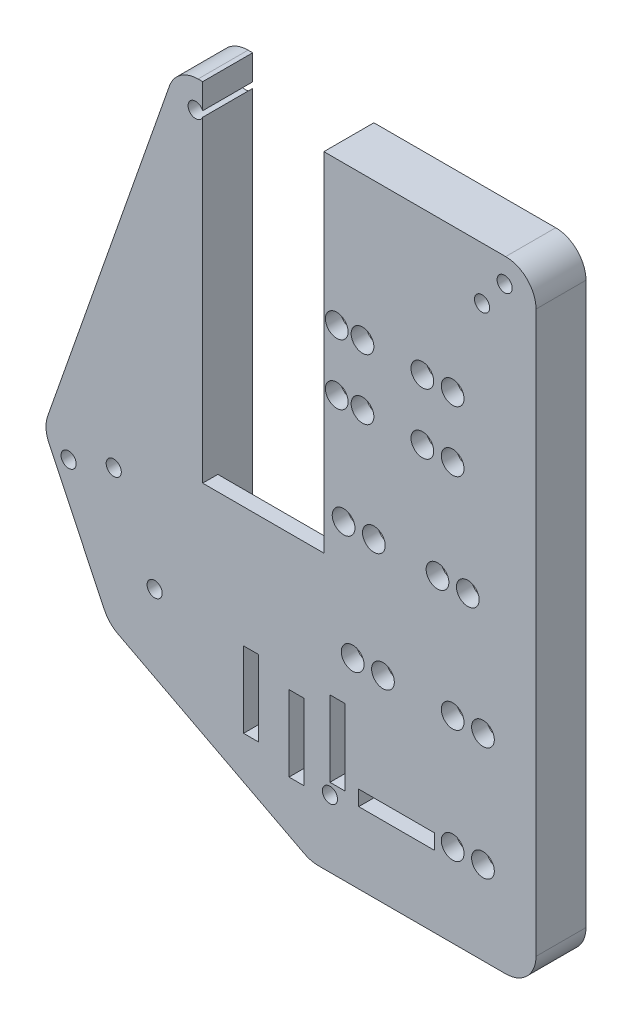
SolidWorks part; units mm, degrees
ref_plane "Front Plane" through (0, 0, 0) normal (0, 0, 1) x (1, 0, 0)
ref_plane "Top Plane" through (0, 0, 0) normal (0, 1, 0) x (1, 0, 0)
ref_plane "Right Plane" through (0, 0, 0) normal (1, 0, 0) x (0, 0, -1)
sketch "Sketch1" plane through (0, 0, 0) normal (0, 0, 1) x (1, 0, 0)
  line L6 (-20.066, -57.15) -> (46.99, -57.15) construction
  line L7 (-12.446, -73.152) -> (46.99, -73.152) construction
  line L8 (-3.3141, 6.35) -> (48.26, 6.35)
  line L9 (53.34, 1.27) -> (53.34, -92.71)
  line L10 (48.26, -97.79) -> (16.847, -97.79)
  line L16 (-8.1072, 2.9529) -> (-28.5162, -55.1739)
  line L18 (-20.066, -57.15) -> (-29.21, -57.15) construction
  line L26 (0, 0) -> (46.99, 0) construction
  line L27 (46.99, 0) -> (46.99, -88.9) construction
  line L28 (46.99, -88.9) -> (17.78, -88.9) construction
  line L29 (17.78, -88.9) -> (-12.446, -73.152) construction
  line L30 (-12.446, -73.152) -> (-20.066, -57.15) construction
  line L31 (-20.066, -57.15) -> (0, 0) construction
  line L32 (46.99, -57.15) -> (46.99, -88.9) construction
  line L33 (17.78, -88.9) -> (15.603, -97.79) construction
  line L34 (-12.446, -73.152) -> (-17.9301, -78.4424) construction
  line L35 (14.4997, -97.2152) -> (-16.7505, -80.9336)
  line L36 (-28.3096, -59.0409) -> (-18.9898, -78.6124)
  arc A0 (53.34, -92.71) -> (48.26, -97.79) centre (48.26, -92.71) cw
  arc A1 (14.4997, -97.2152) -> (16.847, -97.79) centre (16.847, -92.71) ccw
  arc A2 (-16.7505, -80.9336) -> (-18.9898, -78.6124) centre (-14.4033, -76.4284) cw
  arc A3 (-28.5162, -55.1739) -> (-28.3096, -59.0409) centre (-23.723, -56.8568) ccw
  arc A4 (-8.1072, 2.9529) -> (-3.3141, 6.35) centre (-3.3141, 1.27) cw
  arc A5 (48.26, 6.35) -> (53.34, 1.27) centre (48.26, 1.27) cw
  point P13 (53.34, -97.79)
  point P30 (53.34, 6.35)
  dimension "D8" = 5.08
  dimension "D1" = 88.9
  dimension "D2" = 29.21
  dimension "D3" = 59.436
  dimension "D4" = 67.056
  dimension "D5" = 104.14
  dimension "D6" = 82.55
  dimension "D7" = 46.99
  dimension "D13" = 103.76
  dimension "D17" = 108.51
extrude "Boss-Extrude1" add sketch "Sketch1" along normal blind 2.54
sketch "Sketch3" plane through (0, 0, 0) normal (0, 0, 1) x (1, 0, 0)
  line L8 (0, 0) -> (46.99, 0) construction
  line L9 (46.99, 0) -> (46.99, -88.9) construction
  line L10 (46.99, -88.9) -> (17.78, -88.9) construction
  line L11 (17.78, -88.9) -> (-12.446, -73.152) construction
  line L12 (-12.446, -73.152) -> (-20.066, -57.15) construction
  line L13 (-20.066, -57.15) -> (0, 0) construction
sketch "Sketch4" plane through (0, 0, 0) normal (0, 0, -1) x (-1, 0, 0)
  line L0 (-46.99, 0) -> (-46.99, -88.9) construction
  line L1 (0, 0) -> (-46.99, 0) construction
  line L2 (-46.99, -88.9) -> (-17.78, -88.9) construction
  line L8 (-17.78, -1.143) -> (2.54, -1.143)
  line L9 (-17.78, -1.143) -> (-17.78, -51.943)
  line L10 (-17.78, -51.943) -> (2.54, -51.943)
  line L11 (2.54, -1.143) -> (2.54, -51.943)
  circle A0 centre (-39.37, -17.78) radius 1.905
  circle A1 centre (-34.29, -17.78) radius 1.905
  circle A2 centre (-39.37, -27.94) radius 1.905
  circle A3 centre (-34.29, -27.94) radius 1.905
  circle A4 centre (-41.91, -45.72) radius 1.905
  circle A5 centre (-36.83, -45.72) radius 1.905
  circle A6 centre (-44.45, -64.77) radius 1.905
  circle A7 centre (-39.37, -64.77) radius 1.905
  circle A8 centre (-44.45, -83.82) radius 1.905
  circle A9 centre (-39.37, -83.82) radius 1.905
  circle A10 centre (-24.257, -17.78) radius 1.905
  circle A11 centre (-19.939, -17.78) radius 1.905
  circle A12 centre (-24.257, -27.94) radius 1.905
  circle A13 centre (-19.939, -27.94) radius 1.905
  circle A14 centre (-26.162, -45.72) radius 1.905
  circle A15 centre (-21.082, -45.72) radius 1.905
  circle A16 centre (-27.686, -64.77) radius 1.905
  circle A17 centre (-22.606, -64.77) radius 1.905
  point P18 (0, 0)
  dimension "D6" = 3.81
  dimension "D7" = 17.78
  dimension "D11" = 3.81
  dimension "D12" = 3.81
  dimension "D16" = 3.81
  dimension "D17" = 3.81
  dimension "D21" = 3.81
  dimension "D22" = 3.81
  dimension "D30" = 3.81
  dimension "D31" = 3.81
  dimension "D35" = 3.81
  dimension "D36" = 3.81
  dimension "D40" = 3.81
  dimension "D41" = 3.81
  dimension "D45" = 3.81
  dimension "D46" = 3.81
  dimension "D3" = 5.08
  dimension "D5" = 7.62
  dimension "D8" = 5.08
  dimension "D9" = 27.94
  dimension "D10" = 17.78
  dimension "D13" = 5.08
  dimension "D14" = 27.94
  dimension "D15" = 17.78
  dimension "D18" = 5.08
  dimension "D19" = 22.733
  dimension "D20" = 17.78
  dimension "D23" = 5.08
  dimension "D24" = 27.94
  dimension "D25" = 27.051
  dimension "D26" = 50.8
  dimension "D27" = 20.32
  dimension "D28" = 27.94
  dimension "D29" = 45.72
  dimension "D32" = 4.318
  dimension "D33" = 10.16
  dimension "D34" = 5.08
  dimension "D37" = 4.318
  dimension "D38" = 45.72
  dimension "D39" = 45.72
  dimension "D42" = 5.08
  dimension "D43" = 20.828
  dimension "D44" = 2.54
  dimension "D47" = 5.08
  dimension "D48" = 24.13
  dimension "D49" = 2.54
  dimension "D50" = 5.08
  dimension "D51" = 5.08
  dimension "D52" = 24.13
  dimension "D53" = 24.13
  dimension "D54" = 19.304
  dimension "D55" = 24.13
  dimension "D57" = 1.143
  dimension "D58" = 29.21
extrude "Cut-Extrude2" cut sketch "Sketch4" against normal blind 25.4
sketch "Sketch5" plane through (0, 0, 2.54) normal (0, 0, 1) x (1, 0, 0)
  line L0 (-2.54, -1.143) -> (-2.54, 6.35)
  line L1 (48.26, 6.35) -> (-3.3141, 6.35) construction
  line L2 (17.78, -1.143) -> (17.78, 6.35)
  line L3 (17.78, 6.35) -> (-2.54, 6.35)
  line L4 (-2.54, -1.143) -> (17.78, -1.143)
extrude "Cut-Extrude3" cut sketch "Sketch5" against normal blind 5.08
sketch "Sketch6" plane through (0, 0, 2.54) normal (0, 0, 1) x (1, 0, 0)
  line L0 (0, 0) -> (46.99, 0) construction
  line L1 (46.99, 0) -> (46.99, -88.9) construction
  line L2 (17.78, -88.9) -> (17.78, -82.3142) construction
  line L3 (46.99, -88.9) -> (17.78, -88.9) construction
  line L4 (17.78, -88.9) -> (-12.446, -73.152) construction
  line L5 (-12.446, -73.152) -> (-20.066, -57.15) construction
  circle A0 centre (1.6002, -2.4384) radius 1.27
  circle A1 centre (44.2976, -2.4384) radius 1.27
  circle A2 centre (-17.4498, -57.15) radius 1.27
  circle A4 centre (-10.5918, -71.3486) radius 1.27
  circle A5 centre (18.796, -86.5378) radius 1.27
  dimension "D1" = 2.54
  dimension "D3" = 2.54
  dimension "D7" = 2.54
  dimension "D9" = 2.54
  dimension "D11" = 2.54
  dimension "D2" = 2.4384
  dimension "D4" = 2.4384
  dimension "D5" = 2.6924
  dimension "D6" = 45.3898
  dimension "D8" = 2.6162
  dimension "D10" = 2.5866
  dimension "D12" = 1.016
  dimension "D13" = 2.3622
  dimension "D14" = 2.4561
  dimension "D15" = 2.3621
sketch "Sketch8" plane through (0, 0, 2.54) normal (0, 0, 1) x (1, 0, 0)
  line L0 (46.99, 0) -> (46.99, -88.9) construction
  line L1 (23.622, -83.2866) -> (36.322, -83.2866)
  line L2 (23.622, -83.2866) -> (23.622, -85.8266)
  line L3 (23.622, -85.8266) -> (36.322, -85.8266)
  line L4 (36.322, -83.2866) -> (36.322, -85.8266)
  line L5 (0, 0) -> (46.99, 0) construction
  line L7 (18.796, -72.009) -> (21.336, -72.009)
  line L8 (18.796, -72.009) -> (18.796, -84.709)
  line L9 (18.796, -84.709) -> (21.336, -84.709)
  line L10 (21.336, -72.009) -> (21.336, -84.709)
  line L11 (11.938, -74.676) -> (14.478, -74.676)
  line L12 (11.938, -74.676) -> (11.938, -87.376)
  line L13 (11.938, -87.376) -> (14.478, -87.376)
  line L14 (14.478, -74.676) -> (14.478, -87.376)
  line L15 (4.318, -72.136) -> (6.858, -72.136)
  line L16 (4.318, -72.136) -> (4.318, -84.836)
  line L17 (4.318, -84.836) -> (6.858, -84.836)
  line L18 (6.858, -72.136) -> (6.858, -84.836)
  dimension "D1" = 12.7
  dimension "D2" = 2.54
  dimension "D3" = 10.668
  dimension "D4" = 83.2866
  dimension "D5" = 12.7
  dimension "D6" = 2.54
  dimension "D7" = 25.654
  dimension "D8" = 72.009
  dimension "D9" = 12.7
  dimension "D10" = 2.54
  dimension "D11" = 32.512
  dimension "D12" = 74.676
  dimension "D13" = 12.7
  dimension "D14" = 2.54
  dimension "D15" = 72.136
  dimension "D16" = 40.132
extrude "Cut-Extrude5" cut sketch "Sketch8" against normal blind 5.08
sketch "Sketch9" plane through (0, 0, 0) normal (0, 0, -1) x (-1, 0, 0)
  line L0 (-48.26, -97.79) -> (-48.26, 1.27)
  line L1 (-48.26, 1.27) -> (-17.78, 1.27)
  line L2 (-17.78, 1.27) -> (-17.78, 6.35)
  line L3 (-17.78, 6.35) -> (-48.26, 6.35)
  line L4 (-53.34, -92.71) -> (-53.34, 1.27) construction
  line L5 (-53.34, 1.27) -> (-53.34, -92.71)
  line L6 (-17.78, 6.35) -> (-17.78, -51.943) construction
  line L7 (-48.26, 6.35) -> (-17.78, 6.35) construction
  line L9 (2.54, 0.8204) -> (2.54, -82.6092)
  line L12 (2.54, -51.943) -> (2.54, 6.35) construction
  line L13 (2.54, 0.8204) -> (2.54, 6.35)
  line L14 (3.3141, 6.35) -> (2.54, 6.35)
  line L15 (8.1072, 2.9529) -> (28.5162, -55.1739)
  line L17 (28.3096, -59.0409) -> (18.9898, -78.6124)
  line L18 (16.7505, -80.9336) -> (-14.4997, -97.2152)
  line L19 (-16.847, -97.79) -> (-16.847, -92.71)
  line L20 (-16.847, -92.71) -> (2.54, -82.6092)
  arc A0 (-53.34, -92.71) -> (-48.26, -97.79) centre (-48.26, -92.71) ccw
  arc A1 (-16.847, -97.79) -> (-14.4997, -97.2152) centre (-16.847, -92.71) ccw
  arc A2 (16.7505, -80.9336) -> (18.9898, -78.6124) centre (14.4033, -76.4284) ccw
  arc A3 (28.3096, -59.0409) -> (28.5162, -55.1739) centre (23.723, -56.8568) ccw
  arc A4 (3.3141, 6.35) -> (8.1072, 2.9529) centre (3.3141, 1.27) cw
  arc A5 (-48.26, 6.35) -> (-53.34, 1.27) centre (-48.26, 1.27) ccw
  dimension "D3" = 5.08
  dimension "D1" = 5.08
  dimension "D2" = 5.08
extrude "Boss-Extrude2" add sketch "Sketch9" along normal blind 5.842
sketch "Sketch10" plane through (0, 0, 2.54) normal (0, 0, 1) x (1, 0, 0)
  line L0 (48.26, 6.35) -> (17.78, 6.35) construction
  line L1 (53.34, -92.71) -> (53.34, 1.27) construction
  line L2 (-2.54, 6.35) -> (-3.3141, 6.35) construction
  line L3 (-8.1072, 2.9529) -> (-28.5162, -55.1739) construction
  line L4 (-28.3096, -59.0409) -> (-18.9898, -78.6124) construction
  circle A0 centre (48.0822, 2.286) radius 1.27
  circle A1 centre (-3.7187, 1.651) radius 1.27
  circle A2 centre (-25.0123, -59.762) radius 1.27
  dimension "D1" = 2.54
  dimension "D2" = 4.064
  dimension "D3" = 5.2578
  dimension "D4" = 4.699
  dimension "D5" = 4.572
  dimension "D6" = 2.667
  dimension "D7" = 4.826
extrude "Cut-Extrude6" cut sketch "Sketch10" against normal through all both and the other way through all
extrude "Cut-Extrude7" cut sketch "Sketch6" against normal through all both and the other way through all
